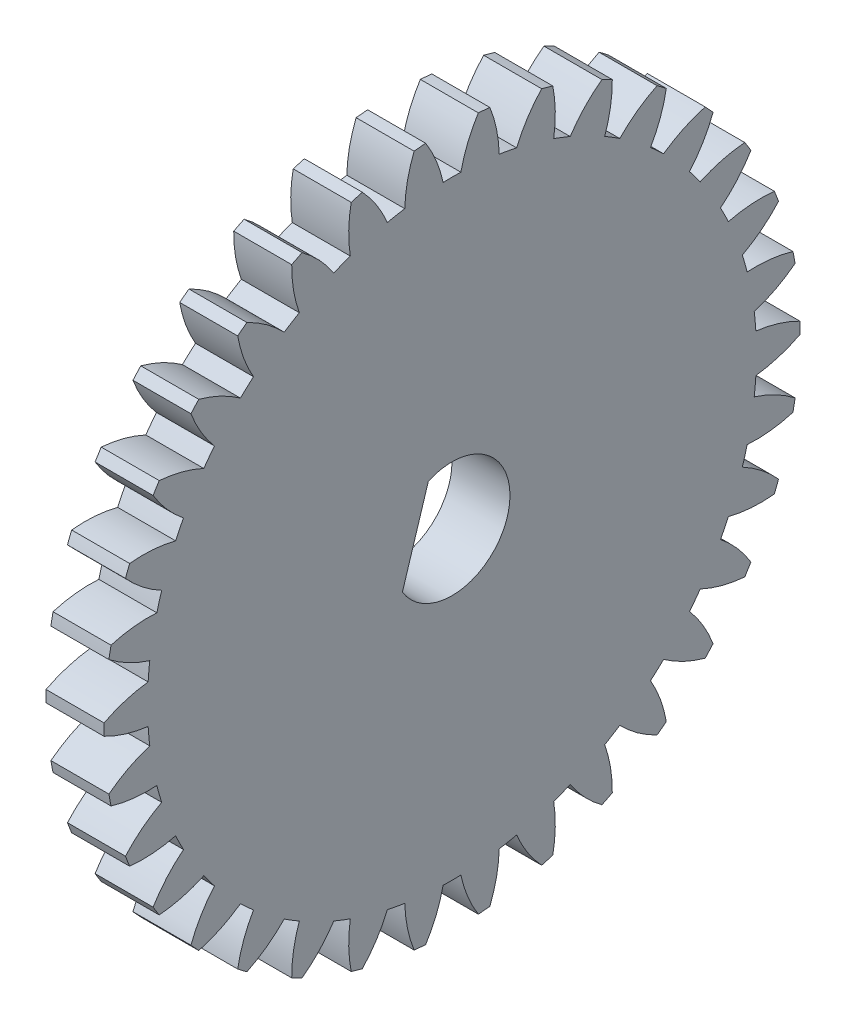
SolidWorks part; units mm, degrees
ref_plane "Plane1" through (0, 0, 0) normal (0, 0, 1) x (1, 0, 0)
ref_plane "Plane2" through (0, 0, 0) normal (0, 1, 0) x (1, 0, 0)
ref_plane "Plane3" through (0, 0, 0) normal (1, 0, 0) x (0, 0, -1)
sketch "HoldingSke" plane through (0, 0, 0) normal (0, 1, 0) x (1, 0, 0)
  line L0 (0, 0) -> (0.829, -0.5592)
  line L1 (-15, 0) -> (100, 0) construction
  line L2 (0, 0) -> (-2.1039, 2.3779)
  line L3 (0, 0) -> (-11.863, 4.5341)
  line L4 (0, 0) -> (7.1596, 4.8292)
  line L5 (0, 0) -> (-46.8476, -17.4728)
  line L6 (0, 0) -> (-2.4869, -1.6779)
  line L7 (-2.1039, 2.3779) -> (8.6586, 51.206)
  line L8 (-76.2, 54.61) -> (-75.7, 54.61)
  line L9 (-71.009, 38.7566) -> (-53.1078, 45.2721)
  line L10 (-76.2, 71.12) -> (104.1128, 71.12)
  line L11 (0, 0) -> (-3, 0)
  line L12 (-76.2, 101.6) -> (-76.162, 101.6)
  line L13 (24.9733, 27.94) -> (52.9518, 28.4284)
  line L14 (24.9733, 27.94) -> (24.9743, 27.94)
  line L15 (24.9733, 27.94) -> (100.4006, 29.5858)
  line L16 (-63.627, -1) -> (-12.827, -1)
  circle A0 centre (0, 0) radius 1.5
  circle A1 centre (0, 0) radius 15.749
  circle A2 centre (0, 0) radius 37.5
  circle A3 centre (0, 0) radius 1.5
  dimension "MHD" = 31.498
  dimension "Hub_dia" = 75
  dimension "Bore" = 3
  dimension "MBD" = 3
  dimension "Num_teeth" = 34
  dimension "Pitch" = 1
  dimension "Overall_len" = 50
  dimension "Show_teeth" = 34
  dimension "Thickness" = 3
  dimension "OAL" = 50.0002
  dimension "T_dim" = 0.5
  dimension "Ap" = 20
  dimension "H" = 19.05
  dimension "Pitch_radius" = 180.3128
  dimension "Width" = 3
  dimension "Backlash" = 0.038
  dimension "Addendum_fac" = 1
  dimension "Dedendum_fac" = 1.25
  dimension "Clearance_fac" = 0.25
  dimension "Dedendum_add" = 0.001
  dimension "Module" = 1
sketch "BasProSke" plane through (0, 0, 0) normal (0, 1, 0) x (1, 0, 0)
  line L0 (-10, 0) -> (60, 0) construction
  line L1 (0, 0) -> (0, 18)
  line L2 (0, 0) -> (3, 0)
  line L3 (3, 0) -> (3, 18)
  line L4 (3, 18) -> (0, 18)
  dimension "Thickness" = 3
  dimension "Diameter" = 36
revolve "Base-Revolve" add sketch "BasProSke" angle 360 about L0
sketch "TooCutSke" plane through (0, 0, 0) normal (1, 0, 0) x (0, 0, -1)
  line L1 (0, 0) -> (0, 107) construction
  line L2 (0, 0) -> (-0.8516, 16.9787) construction
  line L3 (0, 0) -> (-3.1343, 33.8247) construction
  line L4 (-0.8516, 16.9787) -> (-1.5672, 16.9124) construction
  arc A0 (0.4581, 15.7423) -> (-0.4581, 15.7423) centre (0, 0) ccw
  arc A1 (1.3773, 17.9727) -> (-1.3773, 17.9727) centre (0, 0) ccw
  circle A2 centre (0, 0) radius 17 construction
  circle A3 centre (0, 0) radius 15.9748 construction
  arc A4 (-0.4581, 15.7423) -> (-1.3773, 17.9727) centre (-7.1051, 14.3077) ccw
  arc A5 (1.3773, 17.9727) -> (0.4581, 15.7423) centre (7.1051, 14.3077) ccw
  dimension "Root_dia" = 31.498
  dimension "Overcut_dia" = 36.0508
  dimension "Pitch_dia" = 34
  dimension "Base_dia" = 31.9495
  dimension "Flank_rad" = 6.8
  dimension "Half_ang" = 5.294
  dimension "Half_CT" = 0.7186
extrude "ToothCut" cut sketch "TooCutSke" along normal through all
fillet "Breaks" [suppressed] radius 0.02
fillet "RootFillets" [suppressed] radius 0.251
pattern_circular "TeethCuts" count 34 every 10.588 about axis through (-10, 0, 0) along (1, 0, 0) of "ToothCut", "RootFillets", "Breaks"
sketch "HubNeaOneSke" plane through (0, 0, 0) normal (-1, 0, 0) x (0, 0, 1)
  circle A0 centre (0, 0) radius 15.749
  dimension "Diameter" = 31.498
extrude "HubNearOne" [suppressed] add sketch "HubNeaOneSke" along normal blind 47.0002
sketch "HubNeaBotSke" plane through (0, 0, 0) normal (-1, 0, 0) x (0, 0, 1)
  circle A0 centre (0, 0) radius 15.749
  dimension "Diameter" = 31.498
extrude "HubNearBoth" [suppressed] add sketch "HubNeaBotSke" along normal blind 23.5001
ref_plane "FarPln" through (3, 0, 0) normal (1, 0, 0) x (0, 0, -1)
sketch "HubFarSke" plane through (3, 0, 0) normal (1, 0, 0) x (0, 0, -1)
  circle A0 centre (0, 0) radius 15.749
  dimension "Diameter" = 31.498
extrude "HubFar" [suppressed] add sketch "HubFarSke" along normal blind 23.5001
sketch "KeySke" plane through (0, 0, 0) normal (1, 0, 0) x (0, 0, -1)
  line L0 (-0.6, 0) -> (-0.6, 2)
  line L1 (-0.6, 2) -> (0.6, 2)
  line L2 (0.6, 2) -> (0.6, 0)
  line L3 (0, 0) -> (0, 34) construction
  line L4 (-0.6, 0) -> (0.6, 0)
  dimension "Offset" = 2
  dimension "Width" = 1.2
extrude "Keyway" [suppressed] cut sketch "KeySke" along normal mid plane 100.0004
pattern_circular "Keyway2" [suppressed] count 2 every 90 about axis through (-10, 0, 0) along (1, 0, 0)
sketch "Sketch1" plane through (3, 0, 0) normal (1, 0, 0) x (0, 0, -1)
  line L0 (-1.2232, 2.7393) -> (-2.5649, -1.556)
  arc A0 (-2.5649, -1.556) -> (-1.2232, 2.7393) centre (0, 0) ccw
  dimension "D1" = 4.5
  dimension "D2" = 6
extrude "Cut-Extrude1" cut sketch "Sketch1" against normal through all
equation "' \"Module@HoldingSke\" = 6.35"
equation "' \"Num_teeth@HoldingSke\" = 12"
equation "' \"Ap@HoldingSke\" =  20"
equation "' \"Ap@HoldingSke\" = 20"
equation "' \"Width@HoldingSke\" = 0.5 * 25.4"
equation "' \"Hub_dia@HoldingSke\"= 1 * 25.4"
equation "' \"Hub_dia@HoldingSke\" = 1 * 25.4"
equation "' \"Overall_len@HoldingSke\" = 1.0 * 25.4"
equation "' \"Bore@HoldingSke\" = 0.75 * 25.4"
equation "' \"T_dim@HoldingSke\" = 0.1 * 25.4"
equation "' \"Width@KeySke\" = 0.25 * 25.4"
equation "' \"Show_teeth@HoldingSke\" = 13"
equation "' \"Backlash@HoldingSke\" = 0.009 * 25.4"
equation "' \"Addendum_fac@HoldingSke\" = 1.0"
equation "' \"Dedendum_fac@HoldingSke\" = 1.25"
equation "' \"Dedendum_add@HoldingSke\" = 0.00005 * 25.4"
equation "' \"Clearance_fac@HoldingSke\" = 0.25"
equation "\"Pitch@HoldingSke\" = 1 / \"Module@HoldingSke\""
equation "\"Overcut_dia@TooCutSke\" = (\"Num_teeth@HoldingSke\" + 2 * \"Addendum_fac@HoldingSke\") / \"Pitch@HoldingSke\" + 0.002 * 25.4"
equation "\"Pitch_dia@TooCutSke\" = \"Num_teeth@HoldingSke\" / \"Pitch@HoldingSke\""
equation "\"Base_dia@TooCutSke\" = \"Num_teeth@HoldingSke\" / \"Pitch@HoldingSke\" * cos((\"Ap@HoldingSke\"  * 3.14159265 / 180))"
equation "\"Root_dia@TooCutSke\" = (\"Num_teeth@HoldingSke\" + 2) / \"Pitch@HoldingSke\" - 2 * (\"Addendum_fac@HoldingSke\" + \"Dedendum_fac@HoldingSke\") / \"Pitch@HoldingSke\" - \"Dedendum_add@HoldingSke\" * 2"
equation "\"Half_ang@TooCutSke\" = 180 / \"Num_teeth@HoldingSke\""
equation "\"Half_CT@TooCutSke\" = \"Num_teeth@HoldingSke\" / \"Pitch@HoldingSke\" * sin((3.14159265 / 2 / \"Num_teeth@HoldingSke\")) / 2 - 7 * \"Backlash@HoldingSke\" / 4"
equation "\"Flank_rad@TooCutSke\" = \"Num_teeth@HoldingSke\" / \"Pitch@HoldingSke\" / 5"
equation "\"Radius@RootFillets\" = \"Clearance_fac@HoldingSke\" / \"Pitch@HoldingSke\" + \"Dedendum_add@HoldingSke\""
equation "\"Break_rad@Breaks\" = 0.02 / \"Pitch@HoldingSke\""
equation "\"Thickness@HoldingSke\" = \"Width@HoldingSke\""
equation "\"OAL@HoldingSke\" = \"Thickness@HoldingSke\""
equation "\"MHD@HoldingSke\" = (\"Num_teeth@HoldingSke\" + 2) / \"Pitch@HoldingSke\" - 2 * (\"Addendum_fac@HoldingSke\" + \"Dedendum_fac@HoldingSke\")  / \"Pitch@HoldingSke\" - \"Dedendum_add@HoldingSke\" * 2"
equation "\"MBD@HoldingSke\" = (\"Num_teeth@HoldingSke\" + 2) / \"Pitch@HoldingSke\" - 2 * (\"Addendum_fac@HoldingSke\" + \"Dedendum_fac@HoldingSke\")  / \"Pitch@HoldingSke\" - \"Dedendum_add@HoldingSke\" * 2 - 0.002 * 25.4"
equation "\"MHD@HoldingSke\" = ((sgn( \"MHD@HoldingSke\" - \"Hub_dia@HoldingSke\" )-1)*( \"MHD@HoldingSke\" - \"Hub_dia@HoldingSke\" ))/-2+ \"Hub_dia@HoldingSke\""
equation "\"MBD@HoldingSke\" = ((sgn( \"MBD@HoldingSke\" - \"Bore@HoldingSke\" )-1)*( \"MBD@HoldingSke\" - \"Bore@HoldingSke\" ))/-2+ \"Bore@HoldingSke\""
equation "\"OAL@HoldingSke\" = ((sgn( \"OAL@HoldingSke\" - \"Overall_len@HoldingSke\" )+1)*( \"OAL@HoldingSke\" - \"Overall_len@HoldingSke\" ))/2 + \"Overall_len@HoldingSke\" + 0.000002 * 25.4"
equation "\"Num_teeth@TeethCuts\" = int( \"Show_teeth@HoldingSke\" ) + 1"
equation "\"Num_teeth@TeethCuts\" = ((sgn( \"Num_teeth@TeethCuts\" - \"Num_teeth@HoldingSke\" )-1)*( \"Num_teeth@TeethCuts\" - \"Num_teeth@HoldingSke\" ))/-2+ \"Num_teeth@HoldingSke\""
equation "\"Num_teeth@TeethCuts\" = ((sgn( \"Num_teeth@TeethCuts\" - 2.0)+1)*( \"Num_teeth@TeethCuts\" - 2.0))/2 +2.0"
equation "\"Angle@TeethCuts\" = 360.0 / \"Num_teeth@HoldingSke\""
equation "\"Diameter@BasProSke\" = (\"Num_teeth@HoldingSke\" + 2 * \"Addendum_fac@HoldingSke\") / \"Pitch@HoldingSke\""
equation "\"Thickness@BasProSke\"  = \"Thickness@HoldingSke\""
equation "' \"Fillet_rad@BasProSke\" =  \"Thickness@HoldingSke\" * 0.05"
equation "' \"Fillet_rad@BasProSke\" = \"Thickness@HoldingSke\" * 0.05"
equation "\"MHD@HoldingSke\" = ((sgn( \"MHD@HoldingSke\" - \"Root_dia@TooCutSke\" )-1)*( \"MHD@HoldingSke\" - \"Root_dia@TooCutSke\" ))/-2+ \"Root_dia@TooCutSke\""
equation "\"Diameter@HubNeaOneSke\" = \"MHD@HoldingSke\""
equation "\"Length@HubNearOne\" = \"OAL@HoldingSke\" - \"Thickness@BasProSke\""
equation "\"Diameter@HubNeaBotSke\" = \"MHD@HoldingSke\""
equation "\"Length@HubNearBoth\" = ( \"OAL@HoldingSke\" - \"Thickness@BasProSke\" ) / 2.0"
equation "\"Thickness@FarPln\" = \"Thickness@BasProSke\""
equation "\"Diameter@HubFarSke\" = \"MHD@HoldingSke\""
equation "\"Length@HubFar\" = ( \"OAL@HoldingSke\" - \"Thickness@BasProSke\" ) / 2.0"
equation "\"D1\"= \"OAL@HoldingSke\" * 2.0"
equation "\"D1@Keyway\" = \"OAL@HoldingSke\" * 2.0"
equation "\"Offset@KeySke\" = \"T_dim@HoldingSke\" + \"MBD@HoldingSke\" / 2.0"
